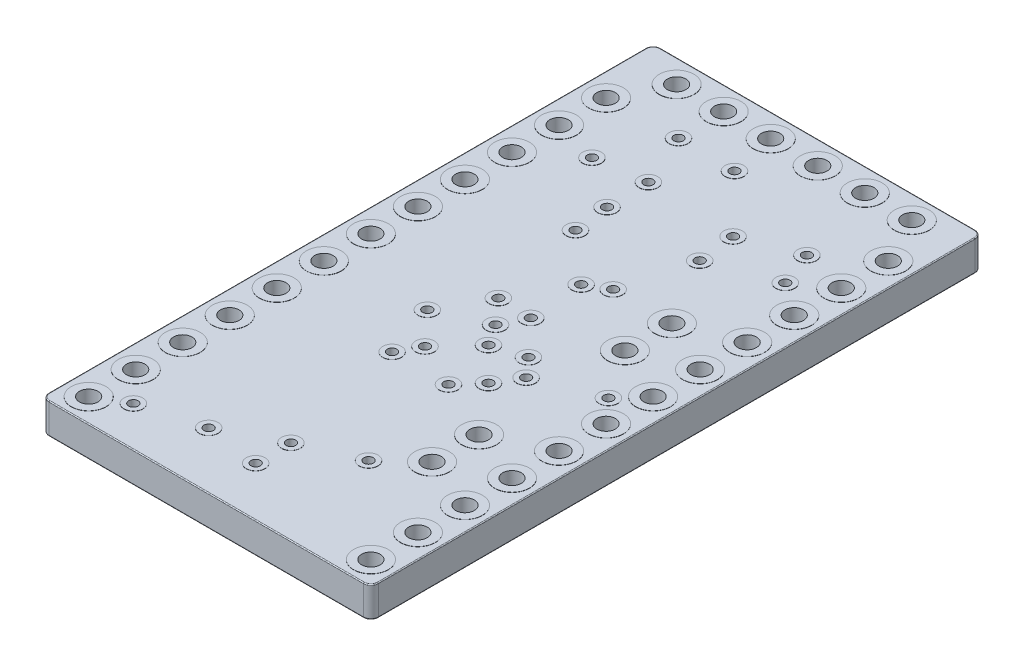
SolidWorks part; units mm, degrees
ref_plane "Front Plane" through (0, 0, 0) normal (0, 0, 1) x (1, 0, 0)
ref_plane "Top Plane" through (0, 0, 0) normal (0, 1, 0) x (1, 0, 0)
ref_plane "Right Plane" through (0, 0, 0) normal (1, 0, 0) x (0, 0, -1)
sketch "Sketch1" plane through (0, 0, 0) normal (0, 1, 0) x (1, 0, 0)
  line L1 (0, 0) -> (17.78, 0)
  line L2 (0, 0) -> (0, 33.02)
  line L3 (0, 33.02) -> (17.78, 33.02)
  line L4 (17.78, 0) -> (17.78, 33.02)
  line L5 (8.89, 33.02) -> (8.89, 0) construction
  line L6 (0, 16.51) -> (17.78, 16.51) construction
  point P84 (8.89, 16.51)
  dimension "D1" = 33.02
  dimension "D2" = 17.78
extrude "Board" add sketch "Sketch1" along normal blind 1.65
sketch "Header Holes" plane through (0, 1.65, 0) normal (0, 1, 0) x (1, 0, 0)
  line L0 (0, 0) -> (17.78, 0) construction
  line L1 (0, 33.02) -> (0, 0) construction
  line L2 (8.89, 33.02) -> (8.89, 0) construction
  line L3 (17.78, 33.02) -> (0, 33.02) construction
  circle A0 centre (1.27, 1.27) radius 0.5
  circle A1 centre (16.51, 1.27) radius 0.5
  circle A2 centre (1.27, 3.81) radius 0.5
  circle A3 centre (16.51, 3.81) radius 0.5
  circle A4 centre (1.27, 6.35) radius 0.5
  circle A5 centre (16.51, 6.35) radius 0.5
  circle A6 centre (1.27, 8.89) radius 0.5
  circle A7 centre (16.51, 8.89) radius 0.5
  circle A8 centre (1.27, 11.43) radius 0.5
  circle A9 centre (16.51, 11.43) radius 0.5
  circle A10 centre (1.27, 13.97) radius 0.5
  circle A11 centre (16.51, 13.97) radius 0.5
  circle A12 centre (1.27, 16.51) radius 0.5
  circle A13 centre (16.51, 16.51) radius 0.5
  circle A14 centre (1.27, 19.05) radius 0.5
  circle A15 centre (16.51, 19.05) radius 0.5
  circle A16 centre (1.27, 21.59) radius 0.5
  circle A17 centre (16.51, 21.59) radius 0.5
  circle A18 centre (1.27, 24.13) radius 0.5
  circle A19 centre (16.51, 24.13) radius 0.5
  circle A20 centre (1.27, 26.67) radius 0.5
  circle A21 centre (16.51, 26.67) radius 0.5
  circle A22 centre (1.27, 29.21) radius 0.5
  circle A23 centre (16.51, 29.21) radius 0.5
  circle A24 centre (13.589, 7.493) radius 0.5
  circle A25 centre (13.589, 10.033) radius 0.5
  circle A26 centre (13.589, 17.907) radius 0.5
  circle A27 centre (13.589, 20.447) radius 0.5
  circle A28 centre (15.24, 31.75) radius 0.5
  circle A29 centre (12.7, 31.75) radius 0.5
  circle A30 centre (10.16, 31.75) radius 0.5
  circle A31 centre (7.62, 31.75) radius 0.5
  circle A32 centre (5.08, 31.75) radius 0.5
  circle A33 centre (2.54, 31.75) radius 0.5
  dimension "D1" = 1.27
  dimension "D2" = 1.27
  dimension "D3" = 1
  dimension "D5" = 1
  dimension "D6" = 7.493
  dimension "D7" = 13.589
  dimension "D8" = 2
  dimension "D9" = 1
  dimension "D10" = 17.907
  dimension "D11" = 13.589
  dimension "D13" = 1
  dimension "D14" = 31.75
  dimension "D15" = 15.24
  dimension "D4" = 12
  dimension "D12" = 2
  dimension "D16" = 6
extrude "Cut-Extrude1" cut sketch "Header Holes" against normal through all
sketch "Sketch3" plane through (0, 1.65, 0) normal (0, 1, 0) x (1, 0, 0)
  circle A0 centre (2.794, 2.159) radius 0.254
  circle A1 centre (5.969, 3.048) radius 0.254
  circle A2 centre (8.89, 4.572) radius 0.254
  circle A3 centre (8.89, 2.667) radius 0.254
  circle A4 centre (11.811, 5.842) radius 0.254
  circle A5 centre (7.366, 11.557) radius 0.254
  circle A6 centre (8.001, 12.7) radius 0.254
  circle A7 centre (10.414, 11.557) radius 0.254
  circle A8 centre (11.43, 12.7) radius 0.254
  circle A9 centre (6.35, 14.478) radius 0.254
  circle A10 centre (12.192, 13.97) radius 0.254
  circle A11 centre (11.303, 14.986) radius 0.254
  circle A12 centre (8.89, 15.621) radius 0.254
  circle A13 centre (9.525, 16.891) radius 0.254
  circle A14 centre (15.367, 15.24) radius 0.254
  circle A15 centre (7.7216, 16.9418) radius 0.254
  circle A16 centre (9.652, 14.478) radius 0.254
  circle A17 centre (9.3218, 19.812) radius 0.254
  circle A18 centre (10.414, 20.447) radius 0.254
  circle A19 centre (6.6294, 22.1996) radius 0.254
  circle A20 centre (6.4008, 24.13) radius 0.254
  circle A21 centre (6.35, 26.416) radius 0.254
  circle A22 centre (3.683, 26.035) radius 0.254
  circle A23 centre (5.1054, 29.2862) radius 0.254
  circle A24 centre (8.1534, 29.2608) radius 0.254
  circle A25 centre (11.4046, 24.13) radius 0.254
  circle A26 centre (11.176, 26.162) radius 0.254
  circle A27 centre (14.7574, 25.4) radius 0.254
  circle A28 centre (14.0462, 27.2796) radius 0.254
  dimension "D4" = 0.508
extrude "Cut-Extrude2" cut sketch "Sketch3" against normal through all
sketch "Sketch4" plane through (0, 1.65, 0) normal (0, 1, 0) x (1, 0, 0)
  circle A0 centre (2.794, 2.159) radius 0.508
  circle A1 centre (5.969, 3.048) radius 0.508
  circle A2 centre (8.89, 4.572) radius 0.508
  circle A3 centre (8.89, 2.667) radius 0.508
  circle A4 centre (11.811, 5.842) radius 0.508
  circle A5 centre (7.366, 11.557) radius 0.508
  circle A6 centre (8.001, 12.7) radius 0.508
  circle A7 centre (10.414, 11.557) radius 0.508
  circle A8 centre (11.43, 12.7) radius 0.508
  circle A9 centre (9.652, 14.478) radius 0.508
  circle A10 centre (6.35, 14.478) radius 0.508
  circle A11 centre (11.303, 14.986) radius 0.508
  circle A12 centre (12.192, 13.97) radius 0.508
  circle A13 centre (15.367, 15.24) radius 0.508
  circle A14 centre (8.89, 15.621) radius 0.508
  circle A15 centre (7.7216, 16.9418) radius 0.508
  circle A16 centre (9.525, 16.891) radius 0.508
  circle A17 centre (9.3218, 19.812) radius 0.508
  circle A18 centre (10.414, 20.447) radius 0.508
  circle A19 centre (6.6294, 22.1996) radius 0.508
  circle A20 centre (6.4008, 24.13) radius 0.508
  circle A21 centre (3.683, 26.035) radius 0.508
  circle A22 centre (6.35, 26.416) radius 0.508
  circle A23 centre (11.4046, 24.13) radius 0.508
  circle A24 centre (11.176, 26.162) radius 0.508
  circle A25 centre (14.0462, 27.2796) radius 0.508
  circle A26 centre (14.7574, 25.4) radius 0.508
  circle A27 centre (8.1534, 29.2608) radius 0.508
  circle A28 centre (5.1054, 29.2862) radius 0.508
  circle A29 centre (2.794, 2.159) radius 0.254
  circle A30 centre (5.969, 3.048) radius 0.254
  circle A31 centre (8.89, 2.667) radius 0.254
  circle A32 centre (8.89, 4.572) radius 0.254
  circle A33 centre (11.811, 5.842) radius 0.254
  circle A34 centre (10.414, 11.557) radius 0.254
  circle A35 centre (7.366, 11.557) radius 0.254
  circle A36 centre (8.001, 12.7) radius 0.254
  circle A37 centre (11.43, 12.7) radius 0.254
  circle A38 centre (6.35, 14.478) radius 0.254
  circle A39 centre (8.89, 15.621) radius 0.254
  circle A40 centre (9.652, 14.478) radius 0.254
  circle A41 centre (11.303, 14.986) radius 0.254
  circle A42 centre (12.192, 13.97) radius 0.254
  circle A43 centre (15.367, 15.24) radius 0.254
  circle A44 centre (9.525, 16.891) radius 0.254
  circle A45 centre (7.7216, 16.9418) radius 0.254
  circle A46 centre (9.3218, 19.812) radius 0.254
  circle A47 centre (10.414, 20.447) radius 0.254
  circle A48 centre (6.6294, 22.1996) radius 0.254
  circle A49 centre (6.4008, 24.13) radius 0.254
  circle A50 centre (6.35, 26.416) radius 0.254
  circle A51 centre (3.683, 26.035) radius 0.254
  circle A52 centre (11.176, 26.162) radius 0.254
  circle A53 centre (11.4046, 24.13) radius 0.254
  circle A54 centre (14.0462, 27.2796) radius 0.254
  circle A55 centre (14.7574, 25.4) radius 0.254
  circle A56 centre (8.1534, 29.2608) radius 0.254
  circle A57 centre (5.1054, 29.2862) radius 0.254
extrude "Boss-Extrude1" add sketch "Sketch4" along normal blind 0.01
sketch "Sketch5" plane through (0, 1.65, 0) normal (0, 1, 0) x (1, 0, 0)
  line L0 (8.89, 33.02) -> (8.89, 0) construction
  line L1 (17.78, 33.02) -> (0, 33.02) construction
  line L2 (0, 0) -> (17.78, 0) construction
  circle A0 centre (1.27, 1.27) radius 0.5
  circle A1 centre (1.27, 1.27) radius 0.94
  circle A2 centre (1.27, 3.81) radius 0.5
  circle A3 centre (1.27, 3.81) radius 0.94
  circle A4 centre (1.27, 6.35) radius 0.5
  circle A5 centre (1.27, 6.35) radius 0.94
  circle A6 centre (1.27, 8.89) radius 0.5
  circle A7 centre (1.27, 8.89) radius 0.94
  circle A8 centre (1.27, 11.43) radius 0.5
  circle A9 centre (1.27, 11.43) radius 0.94
  circle A10 centre (1.27, 13.97) radius 0.5
  circle A11 centre (1.27, 13.97) radius 0.94
  circle A12 centre (1.27, 16.51) radius 0.5
  circle A13 centre (1.27, 16.51) radius 0.94
  circle A14 centre (1.27, 19.05) radius 0.5
  circle A15 centre (1.27, 19.05) radius 0.94
  circle A16 centre (1.27, 21.59) radius 0.5
  circle A17 centre (1.27, 21.59) radius 0.94
  circle A18 centre (1.27, 24.13) radius 0.5
  circle A19 centre (1.27, 24.13) radius 0.94
  circle A20 centre (1.27, 26.67) radius 0.5
  circle A21 centre (1.27, 26.67) radius 0.94
  circle A22 centre (1.27, 29.21) radius 0.5
  circle A23 centre (1.27, 29.21) radius 0.94
  circle A24 centre (16.51, 29.21) radius 0.94
  circle A25 centre (16.51, 29.21) radius 0.5
  circle A26 centre (16.51, 26.67) radius 0.94
  circle A27 centre (16.51, 26.67) radius 0.5
  circle A28 centre (16.51, 24.13) radius 0.94
  circle A29 centre (16.51, 24.13) radius 0.5
  circle A30 centre (16.51, 21.59) radius 0.94
  circle A31 centre (16.51, 21.59) radius 0.5
  circle A32 centre (16.51, 19.05) radius 0.94
  circle A33 centre (16.51, 19.05) radius 0.5
  circle A34 centre (16.51, 16.51) radius 0.94
  circle A35 centre (16.51, 16.51) radius 0.5
  circle A36 centre (16.51, 13.97) radius 0.94
  circle A37 centre (16.51, 13.97) radius 0.5
  circle A38 centre (16.51, 11.43) radius 0.94
  circle A39 centre (16.51, 11.43) radius 0.5
  circle A40 centre (16.51, 8.89) radius 0.94
  circle A41 centre (16.51, 8.89) radius 0.5
  circle A42 centre (16.51, 6.35) radius 0.94
  circle A43 centre (16.51, 6.35) radius 0.5
  circle A44 centre (16.51, 3.81) radius 0.94
  circle A45 centre (16.51, 3.81) radius 0.5
  circle A46 centre (16.51, 1.27) radius 0.94
  circle A47 centre (16.51, 1.27) radius 0.5
  circle A48 centre (2.54, 31.75) radius 0.5
  circle A49 centre (2.54, 31.75) radius 0.94
  circle A50 centre (5.08, 31.75) radius 0.5
  circle A51 centre (5.08, 31.75) radius 0.94
  circle A52 centre (7.62, 31.75) radius 0.5
  circle A53 centre (7.62, 31.75) radius 0.94
  circle A54 centre (10.16, 31.75) radius 0.5
  circle A55 centre (10.16, 31.75) radius 0.94
  circle A56 centre (12.7, 31.75) radius 0.5
  circle A57 centre (12.7, 31.75) radius 0.94
  circle A58 centre (15.24, 31.75) radius 0.5
  circle A59 centre (15.24, 31.75) radius 0.94
  circle A60 centre (13.589, 7.493) radius 0.5
  circle A61 centre (13.589, 10.033) radius 0.5
  circle A62 centre (13.589, 10.033) radius 0.94
  circle A63 centre (13.589, 7.493) radius 0.94
  circle A64 centre (13.589, 17.907) radius 0.5
  circle A65 centre (13.589, 20.447) radius 0.5
  circle A66 centre (13.589, 20.447) radius 0.94
  circle A67 centre (13.589, 17.907) radius 0.94
  dimension "D1" = 1.88
  dimension "D2" = 1
  dimension "D4" = 1.88
  dimension "D6" = 1.88
  dimension "D7" = 1.88
  dimension "D8" = 1.88
  dimension "D9" = 1.88
  dimension "D3" = 12
  dimension "D5" = 6
extrude "Boss-Extrude2" add sketch "Sketch5" along normal blind 0.01
ref_plane "Plane1" through (0, 0.825, 0) normal (0, 1, 0) x (1, 0, 0)
mirror "Mirror1" about plane through (0, 0.825, 0) normal (0, 1, 0) of "Boss-Extrude2", "Boss-Extrude1"
fillet "Fillet1" radius 0.4 4 edges at (0, 0.825, -33.02) (17.78, 0.825, -33.02) (0, 0.825, 0) (17.78, 0.825, 0)
fillet "Fillet2" radius 0.05 16 edges at (17.6628, 0, -0.1172) (8.89, 0, 0) (0.1172, 0, -0.1172) (0, 0, -16.51) (0.1172, 0, -32.9028) (8.89, 0, -33.02) (17.6628, 0, -32.9028) (17.6628, 1.65, -0.1172) (8.89, 1.65, 0) (0.1172, 1.65, -0.1172) (0, 1.65, -16.51) (0.1172, 1.65, -32.9028) (8.89, 1.65, -33.02) (17.6628, 1.65, -32.9028) (17.78, 0, -16.51) (17.78, 1.65, -16.51)
